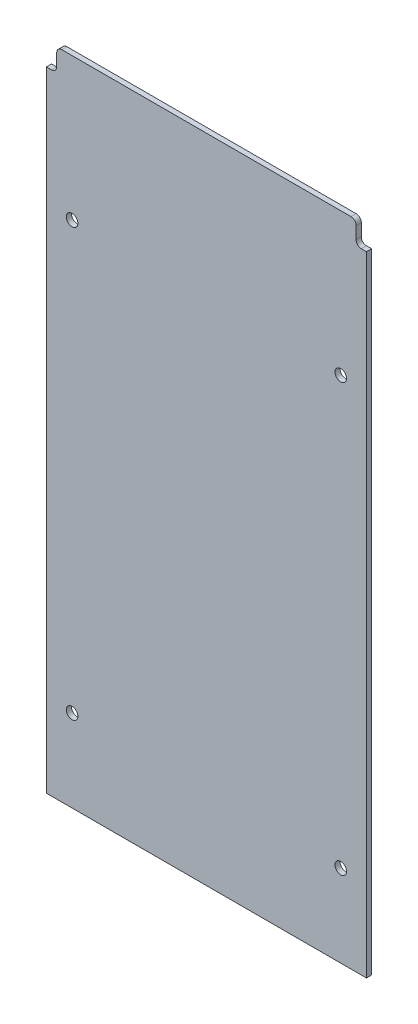
SolidWorks part; units mm, degrees
material "Acrylic (Medium-high impact)"
ref_plane "Front Plane" through (0, 0, 0) normal (0, 0, 1) x (1, 0, 0)
ref_plane "Top Plane" through (0, 0, 0) normal (0, 1, 0) x (1, 0, 0)
ref_plane "Right Plane" through (0, 0, 0) normal (1, 0, 0) x (0, 0, -1)
sketch "Sketch1" plane through (0, 0, 0) normal (0, 0, 1) x (1, 0, 0)
  line L1 (281.197, -361.95) -> (83.6105, -361.95)
  line L2 (281.197, -361.95) -> (281.197, 40.3225)
  line L3 (281.197, 40.3225) -> (83.6105, 40.3225)
  line L4 (83.6105, -361.95) -> (83.6105, 40.3225)
  line L5 (281.197, -361.95) -> (83.6105, 40.3225) construction
  line L6 (281.197, 40.3225) -> (83.6105, -361.95) construction
  line L7 (97.0763, 41.91) -> (153.4312, 41.91) construction
  point P4 (182.4037, -160.8138)
  dimension "D1" = 1.5875
extrude "Boss-Extrude1" add sketch "Sketch1" along normal blind 3.175
sketch "Sketch3" plane through (0, 0, 3.175) normal (0, 0, 1) x (1, 0, 0)
  line L0 (281.197, 40.3225) -> (83.6105, 40.3225) construction
  line L1 (89.9605, 40.3225) -> (83.6105, 40.3225)
  line L2 (89.9605, 40.3225) -> (89.9605, 26.3525)
  line L3 (89.9605, 26.3525) -> (83.6105, 26.3525)
  line L4 (83.6105, 40.3225) -> (83.6105, 26.3525)
  line L5 (89.9605, 40.3225) -> (83.6105, 26.3525) construction
  line L6 (89.9605, 26.3525) -> (83.6105, 40.3225) construction
  line L7 (83.6105, 40.3225) -> (83.6105, -361.95) construction
  line L8 (182.4037, 40.3225) -> (182.4037, -361.95) construction
  line L9 (83.6105, -361.95) -> (281.197, -361.95) construction
  line L10 (274.847, 26.3525) -> (281.197, 40.3225) construction
  line L11 (274.847, 40.3225) -> (281.197, 26.3525) construction
  line L12 (281.197, 40.3225) -> (281.197, 26.3525)
  line L13 (274.847, 26.3525) -> (281.197, 26.3525)
  line L14 (274.847, 40.3225) -> (274.847, 26.3525)
  line L15 (274.847, 40.3225) -> (281.197, 40.3225)
  point P4 (86.7855, 33.3375)
  point P17 (278.022, 33.3375)
  dimension "D1" = 13.97
  dimension "D2" = 6.35
extrude "Cut-Extrude1" cut sketch "Sketch3" against normal through all
fillet "Fillet1" radius 3.175 4 edges at (89.9605, 26.3525, 1.5875) (89.9605, 40.3225, 1.5875) (274.847, 40.3225, 1.5875) (274.847, 26.3525, 1.5875)
hole_wizard "1/4 Clearance Hole1" positions "Sketch4" profile "Sketch5" hole size "1/4" standard "ANSI Inch" end condition up to next
sketch "Sketch4" plane through (0, 0, 3.175) normal (0, 0, 1) x (1, 0, 0)
  point P0 (99.4854, -47.6219)
  point P3 (265.322, -47.625)
  point P6 (265.3221, -311.15)
  point P9 (99.4855, -311.1469)
sketch "Sketch5" plane through (99.4854, -47.6219, 3.175) normal (1, 0, 0) x (0, -1, 0)
  line L0 (0, 0) -> (0, 3.175)
  line L1 (0, 3.175) -> (3.5712, 3.175)
  line L2 (3.5712, 3.175) -> (3.5712, 0)
  line L5 (3.5712, 0) -> (0, 0)
  line L11 (0, -6.35) -> (0, 107.95) construction
  dimension "Thru Hole Dia." = 7.1425
  dimension "Thru Hole Depth" = 3.175
